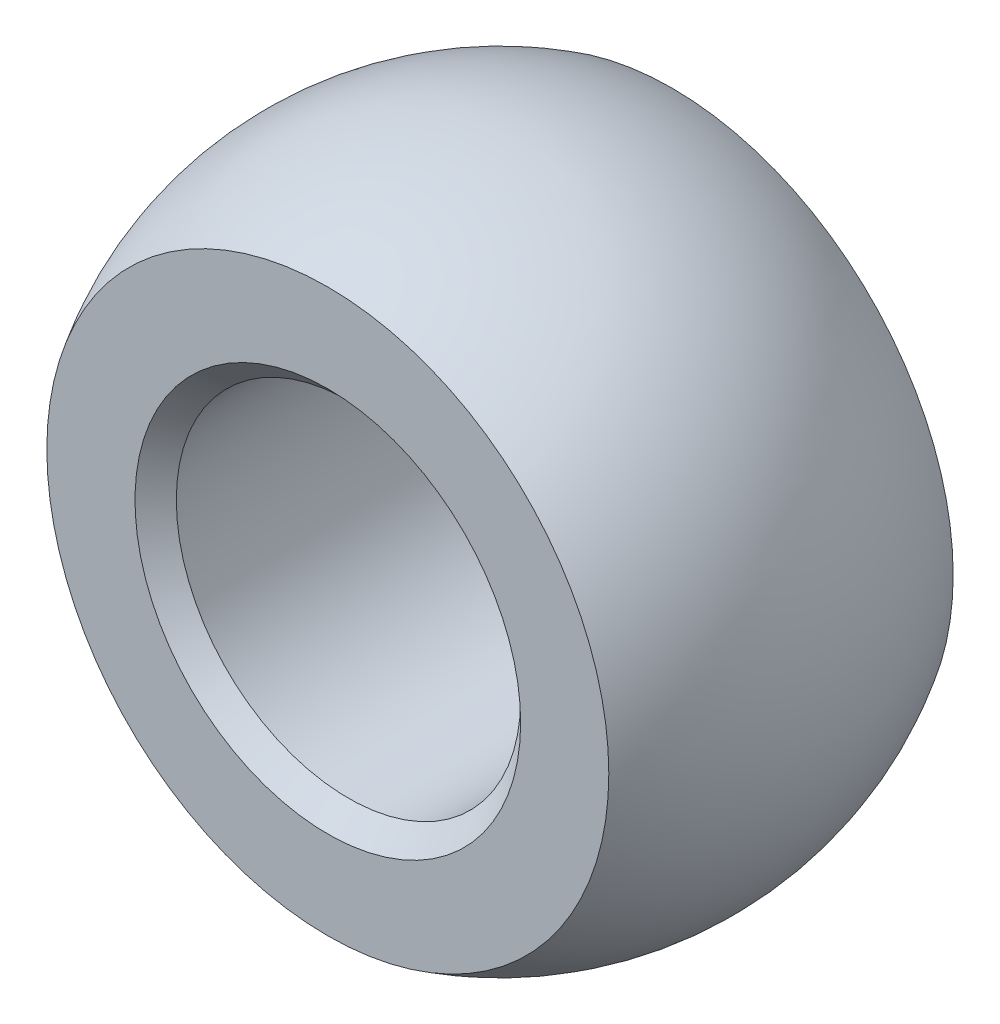
SolidWorks part; units mm, degrees
ref_plane "Front" through (0, 0, 0) normal (0, 0, 1) x (1, 0, 0)
ref_plane "Top" through (0, 0, 0) normal (0, 1, 0) x (1, 0, 0)
ref_plane "Right" through (0, 0, 0) normal (1, 0, 0) x (0, 0, -1)
sketch "Sketch7" plane through (0, 0, 0) normal (0, 0, 1) x (1, 0, 0)
  line L0 (0, 12.1539) -> (0, -12.1539)
  line L1 (0, 22.1145) -> (0, -23.7243) construction
  arc A0 (0, -12.1539) -> (0, 12.1539) centre (0, 0) ccw
  dimension "D2" = 12.1539
sketch "Sketch8" plane through (0, 0, 0) normal (1, 0, 0) x (0, 0, -1)
  line L0 (-6.35, -50.8) -> (6.35, -50.8) construction
  line L2 (-6.35, 50.8) -> (-6.35, -50.8)
  line L4 (6.35, 50.8) -> (6.35, -50.8)
  line L5 (6.35, 50.8) -> (22.225, 50.8)
  line L6 (22.225, 50.8) -> (22.225, -50.8)
  line L7 (22.225, -50.8) -> (6.35, -50.8)
  line L8 (-6.35, -50.8) -> (-22.225, -50.8)
  line L9 (-22.225, -50.8) -> (-22.225, 50.8)
  line L10 (-22.225, 50.8) -> (-6.35, 50.8)
  point P4 (0, -50.8)
  dimension "D1" = 101.6
  dimension "D2" = 44.45
revolve "Revolve1" add sketch "Sketch7" angle 360 about L1
extrude "Cut-Extrude3" cut sketch "Sketch8" against normal through all and the other way through all
sketch "Sketch10" plane through (0, 0, 0) normal (0, 0, 1) x (1, 0, 0)
  circle A1 centre (0, 0) radius 10.3631 construction
  circle A2 centre (0, 0) radius 6.35
  circle A3 centre (0, 0) radius 10.3631 construction
extrude "Cut-Extrude4" cut sketch "Sketch10" against normal through all both and the other way through all
chamfer "Chamfer1" distance 0.762 angle 45 2 edges at (6.35, 0, -6.35) (6.35, 0, 6.35)
scale "Scale1" scale about centroid uniform scaling yes scale factor 0.75
scale "Scale2" scale about centroid uniform scaling yes scale factor 0.666667
